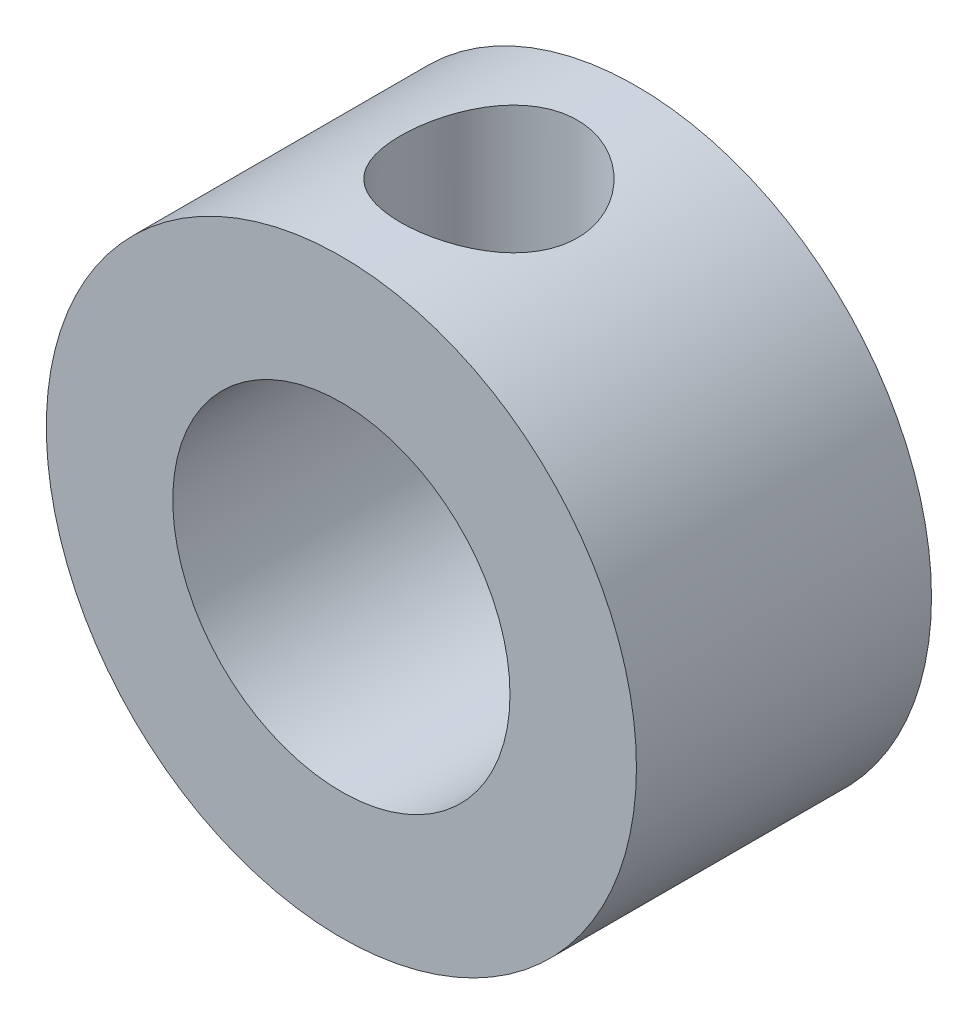
SolidWorks part; units mm, degrees
material "Plain Carbon Steel"
ref_plane "Front Plane" through (0, 0, 0) normal (0, 0, 1) x (1, 0, 0)
ref_plane "Top Plane" through (0, 0, 0) normal (0, 1, 0) x (1, 0, 0)
ref_plane "Right Plane" through (0, 0, 0) normal (1, 0, 0) x (0, 0, -1)
sketch "Sketch1" plane through (0, 0, 0) normal (0, 0, 1) x (1, 0, 0)
  circle A0 centre (0, 0) radius 4
  circle A1 centre (0, 0) radius 7
  dimension "D1" = 8
  dimension "D2" = 14
extrude "Boss-Extrude1" add sketch "Sketch1" along normal blind 7
ref_plane "Plane1" through (0, 7, 0) normal (0, 1, 0) x (1, 0, 0)
hole_wizard "M5x0.8 Tapped Hole1" positions "Sketch3" profile "Sketch2" tap size "M5x0.8" standard "ANSI Metric"
sketch "Sketch3" plane through (0, 7, 0) normal (0, 1, 0) x (1, 0, 0)
  line L0 (0, 0) -> (0, -7) construction
  line L1 (-7, -7) -> (7, -7) construction
  point P8 (0, -3.5)
sketch "Sketch2" plane through (0, 7, 3.5) normal (1, 0, 0) x (0, 0, 1)
  line L0 (0, 0) -> (0, 3)
  line L1 (0, 3) -> (2.1, 3)
  line L2 (2.1, 3) -> (2.1, 0)
  line L5 (2.1, 0) -> (0, 0)
  line L11 (0, -6.35) -> (0, 107.95) construction
  dimension "Thread Major Dia." = 4.2
  dimension "Thru Tap Drill Depth" = 3
